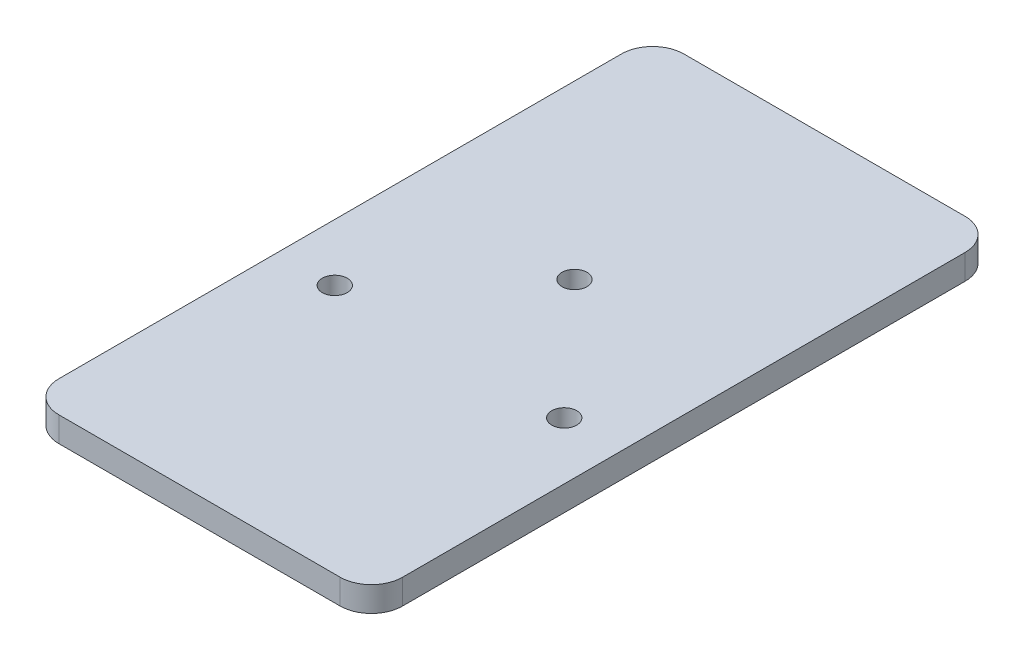
SolidWorks part; units mm, degrees
ref_plane "Front Plane" through (0, 0, 0) normal (0, 0, 1) x (1, 0, 0)
ref_plane "Top Plane" through (0, 0, 0) normal (0, 1, 0) x (1, 0, 0)
ref_plane "Right Plane" through (0, 0, 0) normal (1, 0, 0) x (0, 0, -1)
sketch "Sketch1" plane through (0, 0, 0) normal (0, 1, 0) x (1, 0, 0)
  line L0 (0, 28.965) -> (0, -32.4761) construction
  line L1 (-11.25, -25) -> (11.25, -25)
  line L2 (-13.75, -22.5) -> (-13.75, 22.5)
  line L3 (-11.25, 25) -> (11.25, 25)
  line L4 (13.75, -22.5) -> (13.75, 22.5)
  line L5 (-13.75, -25) -> (13.75, 25) construction
  line L6 (-13.75, 25) -> (13.75, -25) construction
  circle A0 centre (0, 5) radius 1
  circle A1 centre (-9.18, -5) radius 1
  circle A2 centre (9.18, -5) radius 1
  arc A3 (-11.25, 25) -> (-13.75, 22.5) centre (-11.25, 22.5) ccw
  arc A4 (-11.25, -25) -> (-13.75, -22.5) centre (-11.25, -22.5) cw
  arc A5 (13.75, -22.5) -> (11.25, -25) centre (11.25, -22.5) cw
  arc A6 (13.75, 22.5) -> (11.25, 25) centre (11.25, 22.5) ccw
  point P0 (0, 0)
  dimension "D5" = 2
  dimension "D6" = 2
  dimension "D8" = 2.5
  dimension "D1" = 27.5
  dimension "D2" = 50
  dimension "D3" = 20
  dimension "D4" = 10
  dimension "D7" = 4.57
extrude "Boss-Extrude1" add sketch "Sketch1" along normal blind 2
